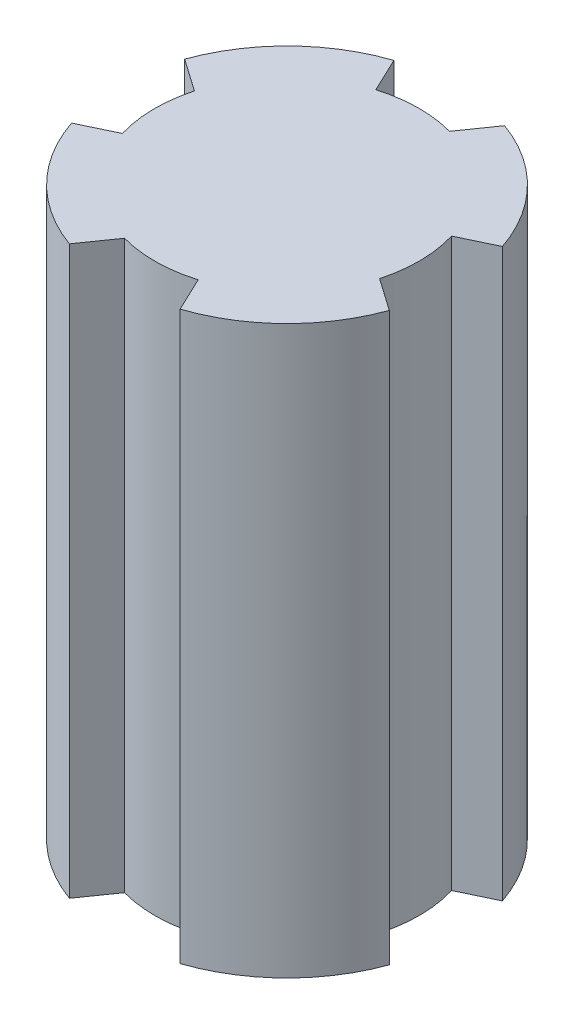
SolidWorks part; units mm, degrees
ref_plane "Front Plane" through (0, 0, 0) normal (0, 0, 1) x (1, 0, 0)
ref_plane "Top Plane" through (0, 0, 0) normal (0, 1, 0) x (1, 0, 0)
ref_plane "Right Plane" through (0, 0, 0) normal (1, 0, 0) x (0, 0, -1)
sketch "Sketch1" plane through (0, 0, 0) normal (0, 1, 0) x (1, 0, 0)
  circle A0 centre (0, 0) radius 4.5
  dimension "D1" = 9
extrude "Boss-Extrude1" add sketch "Sketch1" along normal blind 15
sketch "Sketch2" plane through (0, 15, 0) normal (0, 1, 0) x (1, 0, 0)
  line L0 (-1.0025, 3.3534) -> (-1.4361, 4.2647)
  line L1 (0.9254, 3.3754) -> (1.5255, 4.2335)
  circle A1 centre (0, 0) radius 4.5 construction
  circle A2 centre (0, 0) radius 3.5
  circle A3 centre (0, 0) radius 3.5
  point P9 (0.9254, 3.3534)
  circle M2 centre (0, 0) radius 4.5
  dimension "D1" = 1
extrude "Cut-Extrude1" cut sketch "Sketch2" against normal blind 15 contours A3 L1 L0 M2
pattern_circular "CirPattern1" count 4 over 360 about axis through (0, 0, 0) along (0, 1, 0) of "Cut-Extrude1"
